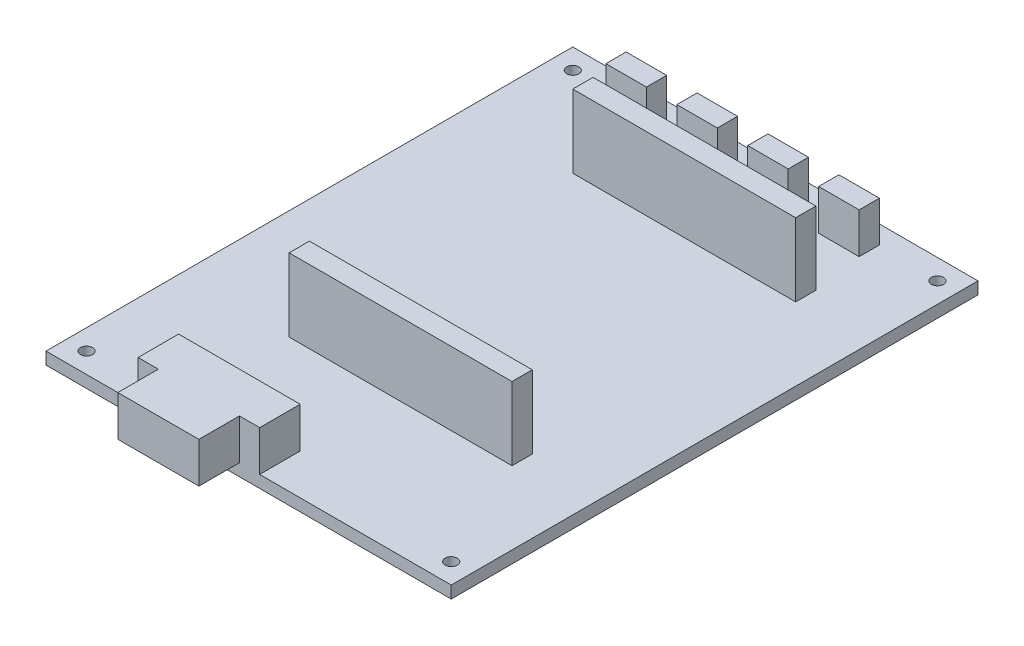
SolidWorks part; units mm, degrees
ref_plane "Face" through (0, 0, 0) normal (0, 0, 1) x (1, 0, 0)
ref_plane "Dessus" through (0, 0, 0) normal (0, 1, 0) x (1, 0, 0)
ref_plane "Droite" through (0, 0, 0) normal (1, 0, 0) x (0, 0, -1)
sketch "Esquisse1" plane through (0, 0, 0) normal (0, 1, 0) x (1, 0, 0)
  line L0 (50, 130) -> (50, 0) construction
  line L1 (0, 0) -> (100, 0)
  line L2 (0, 0) -> (0, 130)
  line L3 (0, 130) -> (100, 130)
  line L4 (100, 0) -> (100, 130)
  line L5 (0, 65) -> (100, 65) construction
  circle A0 centre (5, 125) radius 1.5
  circle A1 centre (95, 125) radius 1.5
  circle A2 centre (95, 5) radius 1.5
  circle A3 centre (5, 5) radius 1.5
  dimension "D3" = 3
  dimension "D1" = 130
  dimension "D2" = 100
  dimension "D4" = 5
  dimension "D5" = 5
extrude "Extrusion1" add sketch "Esquisse1" along normal blind 3
sketch "Esquisse2" plane through (0, 3, 0) normal (0, 1, 0) x (1, 0, 0)
  line L0 (27, 108) -> (27, 33) construction
  line L1 (27, 108) -> (82, 108)
  line L2 (27, 108) -> (27, 103)
  line L3 (27, 103) -> (82, 103)
  line L4 (82, 108) -> (82, 103)
  line L5 (27, 38) -> (82, 38)
  line L6 (27, 38) -> (27, 33)
  line L7 (27, 33) -> (82, 33)
  line L8 (82, 38) -> (82, 33)
  line L9 (100, 130) -> (0, 130) construction
  line L10 (82, 108) -> (82, 33) construction
  line L11 (100, 0) -> (100, 130) construction
  dimension "D1" = 65
  dimension "D2" = 5
  dimension "D3" = 22
  dimension "D4" = 55
  dimension "D5" = 18
extrude "Extrusion2" add sketch "Esquisse2" along normal blind 18
sketch "Esquisse3" plane through (0, 3, 0) normal (0, 1, 0) x (1, 0, 0)
  line L0 (22.7254, 0) -> (22.7254, 10)
  line L1 (0, 0) -> (100, 0) construction
  line L2 (22.7254, 10) -> (52.7254, 10)
  line L3 (37.7254, 10) -> (37.7254, -10) construction
  line L4 (52.7254, 0) -> (52.7254, 10)
  line L5 (47.7254, 0) -> (52.7254, 0)
  line L6 (47.7254, -10) -> (27.7254, -10)
  line L7 (27.7254, -10) -> (27.7254, 0)
  line L8 (27.7254, 0) -> (22.7254, 0)
  line L9 (47.7254, -10) -> (47.7254, 0)
  dimension "D1" = 10
  dimension "D2" = 10
  dimension "D3" = 5
  dimension "D4" = 15
extrude "Extrusion3" add sketch "Esquisse3" along normal blind 10
sketch "Esquisse4" plane through (0, 3, 0) normal (0, 1, 0) x (1, 0, 0)
  line L0 (17.6547, 120.5127) -> (80.1547, 120.5127) construction
  line L1 (17.6547, 125.5127) -> (27.6547, 125.5127)
  line L2 (17.6547, 125.5127) -> (17.6547, 120.5127)
  line L3 (17.6547, 120.5127) -> (27.6547, 120.5127)
  line L4 (27.6547, 125.5127) -> (27.6547, 120.5127)
  line L5 (35.1547, 125.5127) -> (45.1547, 125.5127)
  line L6 (35.1547, 125.5127) -> (35.1547, 120.5127)
  line L7 (35.1547, 120.5127) -> (45.1547, 120.5127)
  line L8 (45.1547, 125.5127) -> (45.1547, 120.5127)
  line L9 (52.6547, 125.5127) -> (62.6547, 125.5127)
  line L10 (52.6547, 125.5127) -> (52.6547, 120.5127)
  line L11 (52.6547, 120.5127) -> (62.6547, 120.5127)
  line L12 (62.6547, 125.5127) -> (62.6547, 120.5127)
  line L13 (70.1547, 125.5127) -> (80.1547, 125.5127)
  line L14 (70.1547, 125.5127) -> (70.1547, 120.5127)
  line L15 (70.1547, 120.5127) -> (80.1547, 120.5127)
  line L16 (80.1547, 125.5127) -> (80.1547, 120.5127)
  dimension "D1" = 10
  dimension "D2" = 5
  dimension "D3" = 7.5
  dimension "D4" = 7.5
  dimension "D5" = 7.5
extrude "Extrusion4" add sketch "Esquisse4" along normal blind 10
